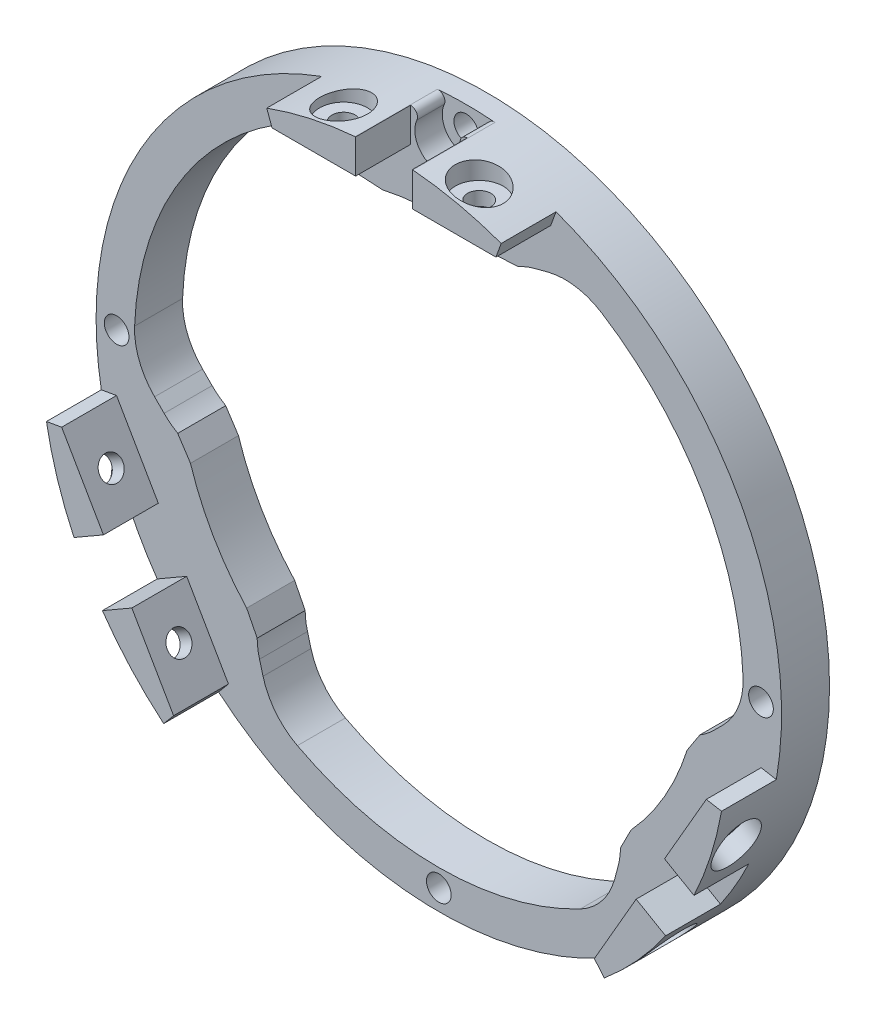
SolidWorks part; units mm, degrees
ref_plane "前视基准面" through (0, 0, 0) normal (0, 0, 1) x (1, 0, 0)
ref_plane "上视基准面" through (0, 0, 0) normal (0, 1, 0) x (1, 0, 0)
ref_plane "右视基准面" through (0, 0, 0) normal (1, 0, 0) x (0, 0, -1)
ref_plane "基准面4" through (0, 150, 0) normal (0, -1, 0) x (1, 0, 0)
sketch "草图1" plane through (0, 150, 0) normal (0, -1, 0) x (1, 0, 0)
  line L0 (650, 7) -> (600, 7)
  line L1 (600, 7) -> (600, 0)
  line L2 (600, 0) -> (650, 0)
  line L3 (650, 0) -> (650, 7)
  line L4 (600, 7) -> (600, 0) construction
revolve "旋转1" add sketch "草图1" angle 360 about L4
sketch "草图2" plane through (0, 0, 7) normal (0, 0, 1) x (1, 0, 0)
  arc A0 (595.8037, 199.8236) -> (596.8015, 198.4211) centre (595.8876, 198.8271) cw
  arc A1 (596.8015, 198.4211) -> (603.1985, 198.4211) centre (600, 197) ccw
  arc A2 (603.1985, 198.4211) -> (604.1963, 199.8236) centre (604.1124, 198.8271) cw
  arc A3 (604.1963, 199.8236) -> (595.8037, 199.8236) centre (600, 150) ccw
extrude "切除-拉伸1" cut sketch "草图2" against normal blind 4
sketch "草图3" plane through (0, 0, 0) normal (0, 0, -1) x (-1, 0, 0)
  line L0 (-613.9181, 188.2398) -> (-619.7348, 189.7943)
  line L1 (-644.3303, 147.1937) -> (-640.0757, 142.9336)
  line L2 (-638.0923, 141.3937) -> (-636.2314, 138.5421)
  line L3 (-628.0385, 124.3516) -> (-626.4994, 121.3142)
  line L4 (-626.1576, 118.8266) -> (-624.5954, 113.012)
  line L5 (-575.4046, 113.012) -> (-573.8424, 118.8266)
  line L6 (-573.5006, 121.3142) -> (-571.9615, 124.3516)
  line L7 (-563.7686, 138.5421) -> (-561.9077, 141.3937)
  line L8 (-559.9243, 142.9336) -> (-555.6697, 147.1937)
  line L9 (-580.2652, 189.7943) -> (-586.0819, 188.2398)
  line L10 (-588.4071, 187.2921) -> (-591.8071, 187.1063)
  line L11 (-608.1929, 187.1063) -> (-611.5929, 187.2921)
  arc A0 (-611.5929, 187.2921) -> (-613.9181, 188.2398) centre (-616.5, 178.5788) ccw
  arc A1 (-619.7348, 189.7943) -> (-644.3303, 147.1937) centre (-600, 150) ccw
  arc A2 (-640.0757, 142.9336) -> (-638.0923, 141.3937) centre (-633, 150) ccw
  arc A3 (-636.2314, 138.5421) -> (-628.0385, 124.3516) centre (-600, 150) ccw
  arc A4 (-626.4994, 121.3142) -> (-626.1576, 118.8266) centre (-616.5, 121.4212) ccw
  arc A5 (-624.5954, 113.012) -> (-575.4046, 113.012) centre (-600, 150) ccw
  arc A6 (-573.8424, 118.8266) -> (-573.5006, 121.3142) centre (-583.5, 121.4212) ccw
  arc A7 (-571.9615, 124.3516) -> (-563.7686, 138.5421) centre (-600, 150) ccw
  arc A8 (-561.9077, 141.3937) -> (-559.9243, 142.9336) centre (-567, 150) ccw
  arc A9 (-555.6697, 147.1937) -> (-580.2652, 189.7943) centre (-600, 150) ccw
  arc A10 (-586.0819, 188.2398) -> (-588.4071, 187.2921) centre (-583.5, 178.5788) ccw
  arc A11 (-591.8071, 187.1063) -> (-608.1929, 187.1063) centre (-600, 150) ccw
extrude "切除-拉伸2" cut sketch "草图3" against normal through all
sketch "草图4" plane through (0, 0, 7) normal (0, 0, 1) x (1, 0, 0)
  line L0 (595.8627, 199.8268) -> (595.8627, 194.8675)
  line L1 (595.8627, 194.8675) -> (583.6696, 194.8675)
  line L2 (583.6696, 194.8675) -> (582.899, 196.9846)
  arc A0 (582.899, 196.9846) -> (595.8037, 199.8236) centre (600, 150) cw
  arc A1 (595.8037, 199.8236) -> (595.8627, 199.8268) centre (595.8876, 198.8271) cw
extrude "凸台-拉伸1" add sketch "草图4" along normal blind 8
sketch "草图5" plane through (0, 0, 7) normal (0, 0, 1) x (1, 0, 0)
  line L0 (617.101, 196.9846) -> (616.3304, 194.8675)
  line L1 (616.3304, 194.8675) -> (604.1373, 194.8675)
  line L2 (604.1373, 194.8675) -> (604.1373, 199.8268)
  arc A0 (604.1963, 199.8236) -> (617.101, 196.9846) centre (600, 150) cw
  arc A1 (604.1373, 199.8268) -> (604.1963, 199.8236) centre (604.1124, 198.8271) cw
extrude "凸台-拉伸2" add sketch "草图5" along normal blind 8
sketch "草图6" plane through (0, 0, 7) normal (0, 0, 1) x (1, 0, 0)
  line L0 (563.2122, 123.9832) -> (569.3088, 113.4237)
  line L1 (569.3088, 113.4237) -> (567.8606, 111.6978)
  line L2 (558.9159, 121.5027) -> (563.2122, 123.9832)
  arc A0 (567.8606, 111.6978) -> (558.9159, 121.5027) centre (600, 150) cw
extrude "凸台-拉伸3" add sketch "草图6" along normal blind 8
sketch "草图7" plane through (0, 0, 7) normal (0, 0, 1) x (1, 0, 0)
  line L0 (559.0749, 131.1493) -> (554.7786, 128.6687)
  line L1 (550.7596, 141.3176) -> (552.9784, 141.7088)
  line L2 (552.9784, 141.7088) -> (559.0749, 131.1493)
  arc A0 (554.7786, 128.6687) -> (550.7596, 141.3176) centre (600, 150) cw
extrude "凸台-拉伸4" add sketch "草图7" along normal blind 8
sketch "草图8" plane through (0, 0, 7) normal (0, 0, 1) x (1, 0, 0)
  line L0 (640.9251, 131.1493) -> (647.0216, 141.7088)
  line L1 (647.0216, 141.7088) -> (649.2404, 141.3176)
  line L2 (645.2214, 128.6687) -> (640.9251, 131.1493)
  arc A0 (649.2404, 141.3176) -> (645.2214, 128.6687) centre (600, 150) cw
extrude "凸台-拉伸5" add sketch "草图8" along normal blind 8
sketch "草图9" plane through (0, 0, 7) normal (0, 0, 1) x (1, 0, 0)
  line L0 (636.7878, 123.9832) -> (641.0841, 121.5027)
  line L1 (632.1394, 111.6978) -> (630.6912, 113.4237)
  line L2 (630.6912, 113.4237) -> (636.7878, 123.9832)
  arc A0 (641.0841, 121.5027) -> (632.1394, 111.6978) centre (600, 150) cw
extrude "凸台-拉伸6" add sketch "草图9" along normal blind 8
ref_plane "基准面5" through (427.994, -247.1024, 0) normal (0.866, -0.5, 0) x (0, 0, -1)
hole_wizard "M3 六角头机械螺钉的柱形沉头孔1" positions "草图11" profile "草图10" counterbore size "M3" standard "ANSI Metric"
sketch "草图11" plane through (427.994, -247.1024, 0) normal (0.866, -0.5, 0) x (0, 0, -1)
  point P0 (-11, 420.0109)
  point P1 (-11, 439.7967)
sketch "草图10" plane through (637.9994, 116.6377, 11) normal (0, 0, 1) x (0.5, 0.866, 0)
  line L0 (0, 0) -> (0, 117.8909)
  line L1 (0, 117.8909) -> (1.7, 117.8909)
  line L3 (1.7, 117.8909) -> (1.7, 2.7221)
  line L4 (1.7, 2.7221) -> (3.5, 2.7221)
  line L5 (3.5, 2.7221) -> (3.5, 0)
  line L7 (3.5, 0) -> (0, 0)
  line L11 (0, -6.35) -> (0, 107.95) construction
  dimension "通孔孔直径" = 3.4
  dimension "通孔孔深度" = 117.8909
  dimension "柱形沉头孔直径" = 7
  dimension "柱形沉头孔深度" = 2.7221
ref_plane "基准面6" through (472.006, 272.5128, 0) normal (-0.866, -0.5, 0) x (0, 0, 1)
hole_wizard "M3 六角头机械螺钉的柱形沉头孔2" positions "草图13" profile "草图12" counterbore size "M3" standard "ANSI Metric"
sketch "草图13" plane through (472.006, 272.5128, 0) normal (-0.866, -0.5, 0) x (0, 0, 1)
  point P0 (11, -160.2033)
  point P1 (11, -179.9891)
sketch "草图12" plane through (552.1077, 133.7727, 11) normal (0, 0, 1) x (0.5, -0.866, 0)
  line L0 (0, 0) -> (0, 117.8909)
  line L1 (0, 117.8909) -> (1.7, 117.8909)
  line L3 (1.7, 117.8909) -> (1.7, 2.7221)
  line L4 (1.7, 2.7221) -> (3.5, 2.7221)
  line L5 (3.5, 2.7221) -> (3.5, 0)
  line L7 (3.5, 0) -> (0, 0)
  line L11 (0, -6.35) -> (0, 107.95) construction
  dimension "通孔孔直径" = 3.4
  dimension "通孔孔深度" = 117.8909
  dimension "柱形沉头孔直径" = 7
  dimension "柱形沉头孔深度" = 2.7221
ref_plane "基准面7" through (0, 199.5896, 0) normal (0, 1, 0) x (1, 0, 0)
hole_wizard "M3 六角头机械螺钉的柱形沉头孔3" positions "草图15" profile "草图14" counterbore size "M3" standard "ANSI Metric"
sketch "草图15" plane through (0, 199.5896, 0) normal (0, 1, 0) x (1, 0, 0)
  point P0 (609.8929, -11)
  point P1 (590.1071, -11)
sketch "草图14" plane through (609.8929, 199.5896, 11) normal (1, 0, 0) x (0, 0, 1)
  line L0 (0, 0) -> (0, 99.5896)
  line L1 (0, 99.5896) -> (1.7, 99.5896)
  line L3 (1.7, 99.5896) -> (1.7, 2.7221)
  line L4 (1.7, 2.7221) -> (3.5, 2.7221)
  line L5 (3.5, 2.7221) -> (3.5, 0)
  line L7 (3.5, 0) -> (0, 0)
  line L11 (0, -6.35) -> (0, 107.95) construction
  dimension "通孔孔直径" = 3.4
  dimension "通孔孔深度" = 99.5896
  dimension "柱形沉头孔直径" = 7
  dimension "柱形沉头孔深度" = 2.7221
hole_wizard "Ø3.6 (3.6) 直径孔1" positions "草图17" profile "草图16" hole size "Ø3.6" standard "ANSI Metric"
sketch "草图17" plane through (0, 0, 0) normal (0, 0, -1) x (-1, 0, 0)
  point P0 (-600, 103)
  point P1 (-647, 150)
  point P2 (-553, 150)
sketch "草图16" plane through (600, 103, 0) normal (1, 0, 0) x (0, 1, 0)
  line L0 (0, 0) -> (0, 15)
  line L1 (0, 15) -> (1.8, 15)
  line L2 (1.8, 15) -> (1.8, 0)
  line L5 (1.8, 0) -> (0, 0)
  line L11 (0, -6.35) -> (0, 107.95) construction
  dimension "通孔孔直径" = 3.6
  dimension "通孔孔深度" = 15
hole_wizard "Ø3.6 (3.6) 直径孔2" positions "草图19" profile "草图18" hole size "Ø3.6" standard "ANSI Metric"
sketch "草图19" plane through (0, 0, 3) normal (0, 0, 1) x (1, 0, 0)
  point P0 (600, 197)
sketch "草图18" plane through (600, 197, 3) normal (1, 0, 0) x (0, -1, 0)
  line L0 (0, 0) -> (0, 3)
  line L1 (0, 3) -> (1.8, 3)
  line L2 (1.8, 3) -> (1.8, 0)
  line L5 (1.8, 0) -> (0, 0)
  line L11 (0, -6.35) -> (0, 107.95) construction
  dimension "通孔孔直径" = 3.6
  dimension "通孔孔深度" = 3
fillet "圆角1" radius 10 6 edges at (644.3303, 147.1937, 3.5) (580.2652, 189.7943, 3.5) (575.4046, 113.012, 3.5) (619.7348, 189.7943, 3.5) (624.5954, 113.012, 3.5) (555.6697, 147.1937, 3.5)
